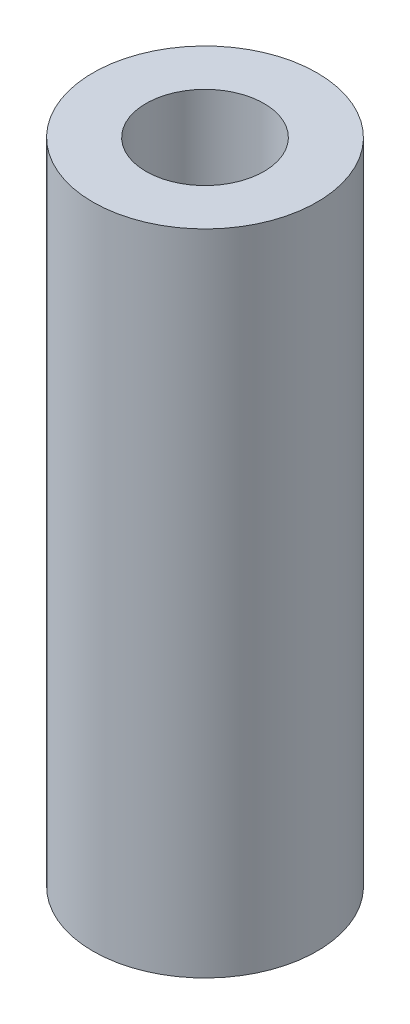
SolidWorks part; units mm, degrees
ref_plane "Front Plane" through (0, 0, 0) normal (0, 0, 1) x (1, 0, 0)
ref_plane "Top Plane" through (0, 0, 0) normal (0, 1, 0) x (1, 0, 0)
ref_plane "Right Plane" through (0, 0, 0) normal (1, 0, 0) x (0, 0, -1)
sketch "Sketch1" plane through (0, 0, 0) normal (0, 1, 0) x (1, 0, 0)
  circle A0 centre (0, 0) radius 5
  circle A1 centre (0, 0) radius 9.5
  dimension "D1" = 10
  dimension "D2" = 19
extrude "Boss-Extrude1" add sketch "Sketch1" along normal blind 55
